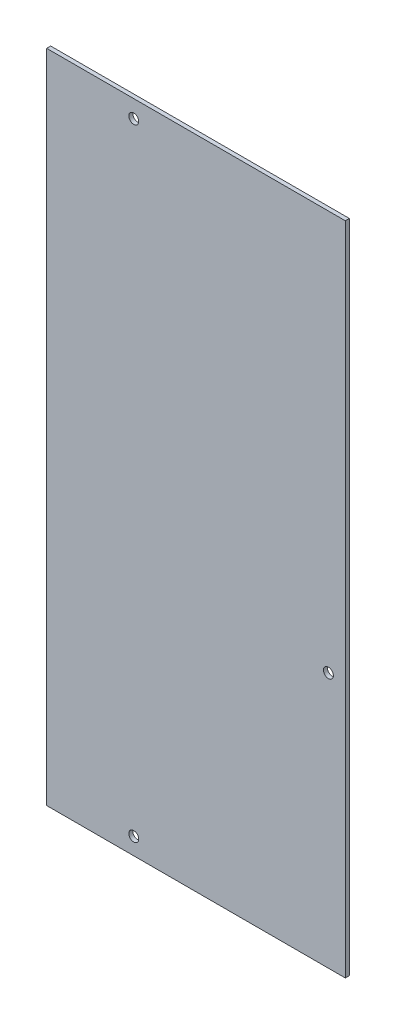
SolidWorks part; units mm, degrees
material "Acrylic (Medium-high impact)"
ref_plane "Front Plane" through (0, 0, 0) normal (0, 0, 1) x (1, 0, 0)
ref_plane "Top Plane" through (0, 0, 0) normal (0, 1, 0) x (1, 0, 0)
ref_plane "Right Plane" through (0, 0, 0) normal (1, 0, 0) x (0, 0, -1)
sketch "Sketch1" plane through (0, 0, 0) normal (0, 0, 1) x (1, 0, 0)
  line L1 (-114.4905, 251.3838) -> (114.4905, 251.3838)
  line L2 (-114.4905, 251.3838) -> (-114.4905, -251.3838)
  line L3 (-114.4905, -251.3838) -> (114.4905, -251.3838)
  line L4 (114.4905, 251.3838) -> (114.4905, -251.3838)
  line L5 (-114.4905, 251.3838) -> (114.4905, -251.3838) construction
  line L6 (-114.4905, -251.3838) -> (114.4905, 251.3838) construction
  point P0 (0, 0)
  dimension "D1" = 228.981
  dimension "D2" = 502.7676
extrude "Boss-Extrude1" add sketch "Sketch1" along normal blind 3.0734
sketch "Sketch2" plane through (0, 0, 3.0734) normal (0, 0, 1) x (1, 0, 0)
  line L0 (-114.4905, -251.3838) -> (114.4905, -251.3838) construction
  line L1 (-114.4905, 251.3838) -> (-114.4905, -251.3838) construction
  line L3 (114.4905, -251.3838) -> (114.4905, 251.3838) construction
  line L4 (0, -251.3838) -> (0, 256.9972) construction
  circle A0 centre (-47.7139, 238.0488) radius 3.81
  circle A1 centre (-47.7139, -238.4044) radius 3.81
  circle A2 centre (101.5111, -55.2789) radius 3.81
  dimension "D1" = 7.62
  dimension "D2" = 12.9794
  dimension "D3" = 66.7766
  dimension "D5" = 12.9794
  dimension "D7" = 196.1049
  dimension "D8" = 508.381
  dimension "D4" = 18.9484
extrude "Cut-Extrude1" cut sketch "Sketch2" against normal through all
equation "\"Height\"= 32in"
equation "\"Width\"= 23in"
equation "\"Depth\"= 20in"
equation "\"Plexi\"= .121in"
equation "\"EBWidth\" = 9in"
equation "\"MagnetThickness\"= 0.125in"
equation "\"MagnetDiameter\"= 12mm"
equation "\"DoorPlexi\" = \"Plexi\""
equation "\"BasePlateThickness\" = 0.5in"
equation "\"BasePlateWidth\" = \"Width\"+\"EBWidth\"-2*\"Plexi\""
equation "\"BasePlateDepth\" = \"TopBarDepth\"+2*\"CornerCube\""
equation "\"Boxsize\" = .75in"
equation "\"BoxsizeHalf\" = \"Boxsize\"/2"
equation "\"Boxinner\" = .625in"
equation "\"CornerCube\" = 0.75in"
equation "\"FingerLength\" = 1.125in"
equation "\"FingerWidth\" = .625in"
equation "\"Cutwidth\"= .016in"
equation "\"Earsize\"= 1in + \"Cutwidth\" /2"
equation "\"Slotsize\" = 1in - \"CutWidth\" / 2"
equation "\"InnerWidth\" = \"Width\" - 2* \"Plexi\""
equation "\"InnerHeight\" = \"Height\" -2 * \"Plexi\""
equation "\"InnerDepth\" = \"Depth\" - 2*\"Plexi\""
equation "\"RearNumHoles\" = 4"
equation "\"RearHolesBorder\" = 2.25"
equation "\"RearHoleSpacing\" = (\"Width\" - 2*\"RearHolesBorder\") / (\"RearNumHoles\"-1)"
equation "\"RearBarLength\" = (\"InnerWidth\"-2*\"CornerCube\")"
equation "\"RearTopNumHoles\" = 4"
equation "\"RearTopHolesBorder\" = 3.1"
equation "\"RearTopHolesSpacing\" = (\"Width\" - 2*\"RearTopHolesBorder\") / (\"RearTopNumHoles\"-1)"
equation "\"SideTopNumHoles\" = 4"
equation "\"SideTopHoleOffset\"=\"CornerCube\"+\"FingerLength\"+\"Plexi\"+.5"
equation "\"SideHorizNumHoles\" = 4"
equation "\"SideHorizHoleBorder\" = 1.50"
equation "\"SideVertBarLength\"=\"Height\"-\"BasePlateThickness\"-2*\"CornerCube\"-\"Plexi\""
equation "\"SideVertNumHoles\" = 4"
equation "\"SideVertHolesBorder\" = \"CornerCube\"+\"FingerLength\"+1.50"
equation "\"SideVertHoleSpacing\" = (\"SideVertBarLength\" - 2*(\"SideVertHolesBorder\"-\"Plexi\"-\"CornerCube\")) / (\"SideVertNumHoles\"-1)"
equation "\"RearSideVertNumHoles\" = 4"
equation "\"RearSideVertHolesBorder\" = 2.4"
equation "\"RearSideVertHoleSpacing\" = (\"SideVertBarLength\" - 2*(\"RearSideVertHolesBorder\"-\"Plexi\"-\"CornerCube\")) / (\"RearSideVertNumHoles\"-1)"
equation "\"RivetDia\" = .228in"
equation "\"SlotDepth\" = \"Plexi\" + 0.75in + .005in"
equation "\"SideSlotWidth\"   = \"Plexi\"+.005in"
equation "\"SidePanelVertSpacing\" = (\"Height\"-2*(1.75-\"Plexi\")) / 5"
equation "\"BottomPanelSideHoleSpacing\" = (\"InnerDepth\"-2*(1.75-\"Plexi\")) / 4"
equation "\"FrontDoorGap\" = .1in"
equation "\"TopDepth\" = \"Depth\"-\"DoorPlexi\"-\"FrontDoorGap\""
equation "\"TopBarDepth\" = \"Depth\"-\"DoorPlexi\"-\"Plexi\"-2*\"MagnetThickness\"-2*\"CornerCube\""
equation "\"CoolerDepth\" = 12in"
equation "\"ShelfGap\" = 0.5in"
equation "\"ShelfDepth\" = \"TopBarDepth\"+\"CornerCube\"-\"CoolerDepth\""
equation "\"ShelfBarDepth\"=\"ShelfDepth\"-2*\"CornerCube\""
equation "\"ShelfWidth\" = \"EBWidth\"-\"ShelfGap\""
equation "\"ShelfBarWidth\" = \"EBWidth\"-\"Boxsize\""
equation "\"ShelfBarWidthShort\" = \"ShelfBarWidth\"-\"Boxsize\"-\"ShelfGap\""
equation "\"IntakeWidth\"=4in"
equation "\"IntakeHeight\"=2in"
equation "\"ExhaustWidth\"=4in"
equation "\"ExhaustHeight\"=2in"
equation "\"VentSpacing\"=7in"
equation "\"AngleBracketLength\"=20mm"
equation "\"AngleBracketWidth\"=.5in"
equation "\"AngleBracketThickness\"=.125in"
equation "\"AngleBracketHolePos\"=15mm"
equation "\"AngleBracketHoleDia\"=\"Rivet3_16Dia\""
equation "\"ShelfBarAngleHole\"=\"ShelfGap\"+\"Boxsize\"+\"AngleBracketHolePosShort\""
equation "\"D1@Sketch1\"=\"EBWidth\"+\"RivNutHeight\""
equation "\"D2@Sketch1\"=\"TopDepth\"+\"RivNutHeight\""
equation "\"D1@Boss-Extrude1\"=\"Plexi\""
equation "\"ComponentMountDia\"=0.1770"
equation "\"ShelfThickness\" = .1250in"
equation "\"SideTopHoleSpacing\" = (\"TopBarDepth\"-2*\"SideTopHoleOffset\") / (\"SideTopNumHoles\"-1)"
equation "\"SideHorizHoleSpacing\" = (\"TopBarDepth\"-2*\"SideHorizHoleBorder\") / (\"SideHorizNumHoles\"-1)"
equation "\"Rivet3_16Dia\" = .191in"
equation "\"BinderPostDia\" = .228in"
equation "\"ShelfHeight1\" = 13in"
equation "\"ShelfHeight2\" = 24in"
equation "\"VentVertLocation\"=12.75in"
equation "\"AngleBracketLengthShort\"=.625in"
equation "\"AngleBracketLengthLong\"=1in"
equation "\"AngleBracketHolePosShort\"=.358in"
equation "\"AngleBracketHolePosLong\"=.7in"
equation "\"PSBracketThickness\" = .0641in"
equation "\"EBForwardMountOffset\" = 4.0in"
equation "\"EBForwardMount\" = 2*\"Boxsize\"+\"CoolerDepth\"+\"EBForwardMountOffset\""
equation "\"EBRearwardMountOffset\" = 1.5in"
equation "\"EBRearwardMount\"= \"Boxsize\"+\"EBRearwardMountOffset\""
equation "\"MagSealWidth\" = \"InnerWidth\""
equation "\"MagSealHeight\" = \"Height\"-\"BasePlateThickness\"-\"Plexi\""
equation "\"MagWidth\" = .500in"
equation "\"SiliconeSealOD\" = .3125in"
equation "\"SiliconeSealID\" = .1875in"
equation "\"SiliconeSealWidth\" = \"MagSealWidth\" - 2*\"MagWidth\"-\"SiliconeSealOD\""
equation "\"SiliconeSealHeigth\" = \"MagSealHeight\" - 2*\"MagWidth\"-\"SiliconeSealOD\""
equation "\"HooknLoopThick\" = .085in"
equation "\"HooknLoopWidth\" = 0.75in"
equation "\"HooknLoopHeigth\" = 0.75in"
equation "\"RivNutHeight\" = 0.015in"
equation "\"D2@Sketch2\"=\"RivNutHeight\"+\"Plexi\"+\"BoxsizeHalf\""
equation "\"D3@Sketch2\"=\"ShelfBarWidth\"/3-\"Plexi\""
equation "\"D5@Sketch2\"=\"Plexi\"+\"BoxsizeHalf\"+\"RivNutHeight\""
equation "\"D7@Sketch2\"=\"Plexi\"+\"RivNutHeight\"+\"CornerCube\"+\"SideTopHoleOffset\"+\"SideTopHoleSpacing\""
equation "\"D8@Sketch2\"=\"Depth\"+\"RivNutHeight\""
equation "\"D4@Sketch2\"=\"MagnetThickness\"*2+\"BoxsizeHalf\"+\"Plexi\""
